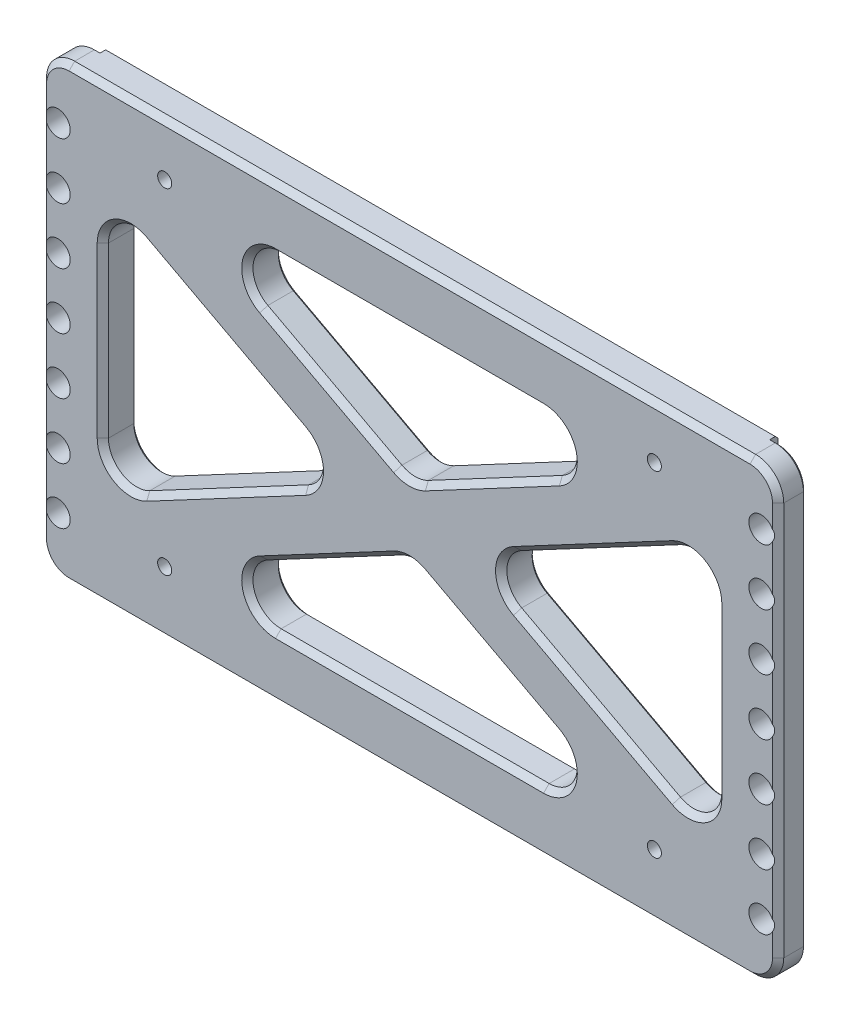
SolidWorks part; units mm, degrees
material "6061 合金"
ref_plane "前视基准面" through (0, 0, 0) normal (0, 0, 1) x (1, 0, 0)
ref_plane "上视基准面" through (0, 0, 0) normal (0, 1, 0) x (1, 0, 0)
ref_plane "右视基准面" through (0, 0, 0) normal (1, 0, 0) x (0, 0, -1)
sketch "草图3" plane through (0, 0, 0) normal (0, 0, 1) x (1, 0, 0)
  line L0 (-57.5, -11.5) -> (57.5, -11.5) construction
  line L1 (-65.5, -11.5) -> (65.5, -11.5)
  line L2 (-65.5, -91.5) -> (65.5, -91.5)
  line L3 (65.5, -6) -> (65.5, -101.8916) construction
  line L4 (-65.5, -101.8916) -> (-65.5, -6) construction
  line L5 (65.5, -11.5) -> (65.5, -91.5)
  line L6 (-65.5, -91.5) -> (-65.5, -11.5)
  line L7 (-57.5, -11.5) -> (57.5, -11.5) construction
  line L8 (-57.5, -91.5) -> (57.5, -91.5) construction
  dimension "D1" = 80
extrude "凸台-拉伸3" add sketch "草图3" along normal blind 5
sketch "草图4" plane through (0, 0, 5) normal (0, 0, 1) x (1, 0, 0)
  line L0 (-65.5, -91.5) -> (65.5, -91.5) construction
  line L1 (59.5, -91.5) -> (-59.5, -91.5)
  line L2 (59.5, -91.5) -> (59.5, -11.5)
  line L3 (59.5, -11.5) -> (-59.5, -11.5)
  line L4 (-59.5, -91.5) -> (-59.5, -11.5)
  line L5 (59.5, -11.5) -> (59.5, -101.8916) construction
  line L6 (58.5, -11.5) -> (-58.5, -11.5) construction
  line L7 (65.5, -11.5) -> (-65.5, -11.5) construction
extrude "凸台-拉伸4" add sketch "草图4" against normal blind 6
fillet "圆角2" radius 5 4 edges at (65.5, -11.5, 2.5) (-65.5, -11.5, 2.5) (-65.5, -91.5, 2.5) (65.5, -91.5, 2.5)
chamfer "倒角1" distance 1 angle 45 8 edges at (-65.5, -51.5, 5) (-64.0355, -90.0355, 5) (-64.0355, -12.9645, 5) (0, -91.5, 5) (0, -11.5, 5) (64.0355, -90.0355, 5) (64.0355, -12.9645, 5) (65.5, -51.5, 5)
sketch "草图5" plane through (0, 0, 5) normal (0, 0, 1) x (1, 0, 0)
  line L4 (-54.5, -22.5) -> (54.5, -80.5)
  line L5 (-54.5, -80.5) -> (54.5, -22.5)
  line L6 (-52.1513, -84.914) -> (56.8487, -26.914)
  line L7 (-56.8487, -26.914) -> (52.1513, -84.914)
  line L8 (-54.5, -22.5) -> (-54.5, -80.5)
  line L9 (-54.5, -80.5) -> (54.5, -80.5)
  line L10 (54.5, -80.5) -> (54.5, -22.5)
  line L11 (54.5, -22.5) -> (-54.5, -22.5)
  line L12 (-54.5, -22.5) -> (-54.5, -80.5)
  line L13 (-54.5, -80.5) -> (54.5, -80.5)
  line L14 (54.5, -80.5) -> (54.5, -22.5)
  line L15 (54.5, -22.5) -> (-54.5, -22.5)
  line L16 (-56.8487, -76.086) -> (52.1513, -18.086)
  line L17 (-52.1513, -18.086) -> (56.8487, -76.086)
  dimension "D2" = 5
  dimension "D1" = 10
  dimension "D3" = 5
extrude "切除-拉伸1" cut sketch "草图5" against normal blind 6 contours L12 L16 L7 | L15 L17 L16 | L6 L17 L14 | L6 L13 L7
fillet "圆角3" radius 5 12 edges at (54.5, -28.1638, 2) (54.5, -74.8362, 2) (10.644, -51.5, 2) (0, -45.8362, 2) (-43.856, -22.5, 2) (43.856, -22.5, 2) (-10.644, -51.5, 2) (-54.5, -74.8362, 2) (-54.5, -28.1638, 2) (0, -57.1638, 2) (43.856, -80.5, 2) (-43.856, -80.5, 2)
chamfer "倒角2" distance 1 angle 45 24 edges at (-52.0745, -70.7981, 5) (-54.5, -51.5, 5) (-33.0453, -63.4199, 5) (-52.0745, -32.2019, 5) (-16.288, -51.5, 5) (-33.0453, -39.5801, 5) (28.6667, -26.2896, 5) (0, -22.5, 5) (14.2564, -38.2502, 5) (-28.6667, -26.2896, 5) (0, -45.1724, 5) (-14.2564, -38.2502, 5) (52.0745, -32.2019, 5) (33.0453, -39.5801, 5) (54.5, -51.5, 5) (16.288, -51.5, 5) (52.0745, -70.7981, 5) (33.0453, -63.4199, 5) (-28.6667, -76.7104, 5) (-14.2564, -64.7498, 5) (0, -80.5, 5) (0, -57.8276, 5) (28.6667, -76.7104, 5) (14.2564, -64.7498, 5)
sketch "草图6" plane through (0, 0, 5) normal (0, 0, 1) x (1, 0, 0)
  line L0 (65.5, -51.5) -> (59.5, -51.5) construction
  line L1 (65.5, -16.5) -> (65.5, -86.5) construction
  line L2 (62.5, -41.5) -> (62.5, -61.5) construction
  line L3 (62.5, -31.5) -> (62.5, -71.5) construction
  line L4 (62.5, -21.5) -> (62.5, -81.5) construction
  circle A0 centre (62.5, -21.5) radius 2.2
  circle A1 centre (62.5, -31.5) radius 2.2
  circle A2 centre (62.5, -41.5) radius 2.2
  circle A3 centre (62.5, -51.5) radius 2.2
  circle A4 centre (62.5, -61.5) radius 2.2
  circle A5 centre (62.5, -71.5) radius 2.2
  circle A6 centre (62.5, -81.5) radius 2.2
  point P7 (62.5, -51.5)
  point P11 (62.5, -51.5)
  point P14 (62.5, -51.5)
  dimension "D1" = 7
extrude "切除-拉伸2" cut sketch "草图6" against normal blind 11
mirror "镜向1" about plane through (0, 0, 0) normal (1, 0, 0) of "切除-拉伸2"
sketch "草图7" plane through (0, 0, 5) normal (0, 0, 1) x (1, 0, 0)
  line L0 (0, -90.5) -> (0, -50.52) construction
  line L1 (-60.5, -90.5) -> (60.5, -90.5) construction
  line L3 (-43.51, -80.29) -> (43.51, -80.29)
  line L4 (-43.51, -80.29) -> (-43.51, -20.75)
  line L5 (-43.51, -20.75) -> (43.51, -20.75)
  line L6 (43.51, -80.29) -> (43.51, -20.75)
  line L7 (-43.51, -80.29) -> (43.51, -20.75) construction
  line L8 (-43.51, -20.75) -> (43.51, -80.29) construction
hole_wizard "M3 螺纹孔1" positions "草图8" profile "草图9" tap size "M3" standard "GB"
sketch "草图8" plane through (0, 0, 5) normal (0, 0, 1) x (1, 0, 0)
  point P0 (-43.51, -20.75)
  point P3 (43.51, -20.75)
  point P6 (43.51, -80.29)
  point P9 (-43.51, -80.29)
sketch "草图9" plane through (-43.51, -20.75, 5) normal (1, 0, 0) x (0, -1, 0)
  line L0 (0, 0) -> (0, 8.2511)
  line L1 (0, 8.2511) -> (1.25, 7.5)
  line L2 (1.25, 7.5) -> (1.25, 0)
  line L5 (1.25, 0) -> (0, 0)
  line L10 (0, 8.2511) -> (-1.25, 7.5) construction
  line L11 (0, -6.35) -> (0, 107.95) construction
  dimension "螺纹孔钻头直径" = 2.5
  dimension "螺纹孔钻头深度" = 7.5
  dimension "导头角度" = 118
cosmetic thread "孔螺蚊线1" parameters "D1"=6, "D2"=3
cosmetic thread "孔螺蚊线2" parameters "D1"=6, "D2"=3
cosmetic thread "孔螺蚊线3" parameters "D1"=6, "D2"=3
cosmetic thread "孔螺蚊线4" parameters "D1"=6, "D2"=3
chamfer "倒角3" distance 0.5 angle 45 36 edges at (-60, -11.5, 0) (-64.0355, -12.9645, 0) (-60, -91.5, 0) (-65.5, -51.5, 0) (-64.0355, -90.0355, 0) (0, -91.5, -1) (60, -91.5, 0) (64.0355, -90.0355, 0) (60, -11.5, 0) (65.5, -51.5, 0) (64.0355, -12.9645, 0) (0, -11.5, -1) (52.0745, -70.7981, -1) (33.0453, -63.4199, -1) (54.5, -51.5, -1) (16.288, -51.5, -1) (52.0745, -32.2019, -1) (33.0453, -39.5801, -1) (0, -80.5, -1) (28.6667, -76.7104, -1) (-28.6667, -76.7104, -1) (14.2564, -64.7498, -1) (-14.2564, -64.7498, -1) (0, -57.8276, -1) (-52.0745, -70.7981, -1) (-54.5, -51.5, -1) (-33.0453, -63.4199, -1) (-52.0745, -32.2019, -1) (-16.288, -51.5, -1) (-33.0453, -39.5801, -1) (0, -45.1724, -1) (14.2564, -38.2502, -1) (-14.2564, -38.2502, -1) (28.6667, -26.2896, -1) (-28.6667, -26.2896, -1) (0, -22.5, -1)
